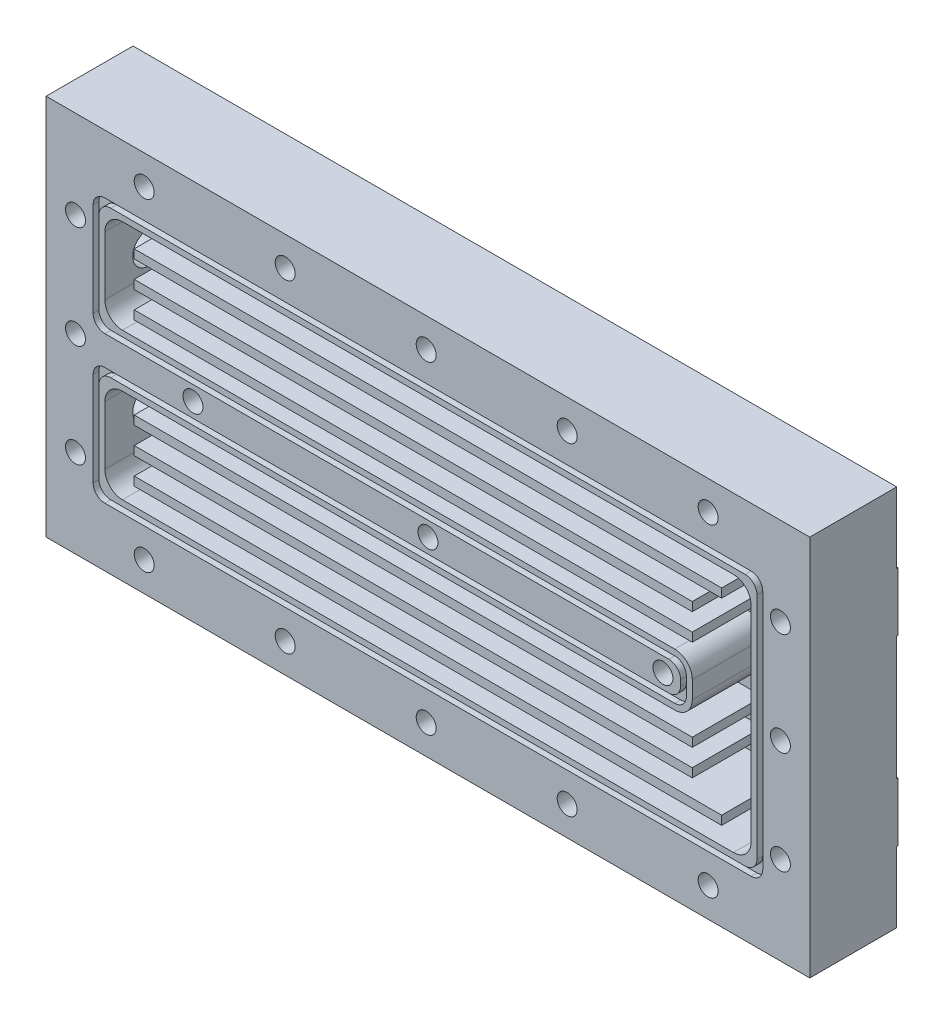
SolidWorks part; units mm, degrees
ref_plane "Plan de face" through (0, 0, 0) normal (0, 0, 1) x (1, 0, 0)
ref_plane "Plan de dessus" through (0, 0, 0) normal (0, 1, 0) x (1, 0, 0)
ref_plane "Plan de droite" through (0, 0, 0) normal (1, 0, 0) x (0, 0, -1)
sketch "Esquisse1" plane through (0, 0, 0) normal (0, 0, 1) x (1, 0, 0)
  line L1 (0, 0) -> (130, 0)
  line L2 (0, 0) -> (0, 65)
  line L3 (0, 65) -> (130, 65)
  line L4 (130, 0) -> (130, 65)
  dimension "D1" = 130
  dimension "D2" = 65
extrude "Boss.-Extru.1" add sketch "Esquisse1" along normal blind 14.8
sketch "Esquisse13" plane through (0, 0, 0) normal (0, 0, -1) x (-1, 0, 0)
  line L0 (-130, 0) -> (-130, 65) construction
  line L1 (-130, 53) -> (0, 53)
  line L2 (-130, 53) -> (-130, 43)
  line L3 (-130, 43) -> (0, 43)
  line L4 (0, 53) -> (0, 43)
  line L5 (0, 65) -> (0, 0) construction
  line L6 (-130, 65) -> (0, 65) construction
  line L7 (-130, 22) -> (0, 22)
  line L8 (-130, 22) -> (-130, 12)
  line L9 (-130, 12) -> (0, 12)
  line L10 (0, 22) -> (0, 12)
  line L11 (0, 0) -> (-130, 0) construction
  dimension "D1" = 10
  dimension "D2" = 10
  dimension "D3" = 12
  dimension "D4" = 12
extrude "Boss.-Extru.3" add sketch "Esquisse13" along normal blind 0.2
sketch "Esquisse2" plane through (0, 0, 14.8) normal (0, 0, 1) x (1, 0, 0)
  line L0 (-5.5409, 60) -> (136.6271, 60) construction
  line L1 (-5.5409, 5) -> (135.6371, 5) construction
  line L2 (130, 65) -> (0, 65) construction
  line L3 (0, 0) -> (130, 0) construction
  line L4 (0, 65) -> (0, 0) construction
  circle A0 centre (16.7, 60) radius 1
  circle A1 centre (40.7, 60) radius 1
  circle A2 centre (64.7, 60) radius 1
  circle A3 centre (88.7, 60) radius 1
  circle A4 centre (112.7, 60) radius 1
  circle A6 centre (16.7, 5) radius 1
  circle A7 centre (40.7, 5) radius 1
  circle A8 centre (64.7, 5) radius 1
  circle A9 centre (88.7, 5) radius 1
  circle A10 centre (112.7, 5) radius 1
  point P19 (0, 0)
  point P33 (0, 0)
  point P34 (49.9853, 3.1391)
  dimension "D3" = 16.7
  dimension "D9" = 24
  dimension "D1" = 5
  dimension "D2" = 5
  dimension "D4" = 24
  dimension "D5" = 24
  dimension "D6" = 24
  dimension "D7" = 24
  dimension "D8" = 24
  dimension "D10" = 24
  dimension "D11" = 24
  dimension "D12" = 16.7
hole_wizard "Dégagement M31" positions "Esquisse14" profile "Esquisse15" hole size "M3" standard "ISO" end condition through all
sketch "Esquisse14" plane through (0, 0, 14.8) normal (0, 0, 1) x (1, 0, 0)
  point P0 (16.7, 60)
  point P3 (40.7, 60)
  point P6 (64.7, 60)
  point P9 (88.7, 60)
  point P12 (112.7, 60)
  point P21 (112.7, 5)
  point P24 (88.7, 5)
  point P27 (64.7, 5)
  point P30 (40.7, 5)
  point P33 (16.7, 5)
sketch "Esquisse15" plane through (16.7, 60, 14.8) normal (1, 0, 0) x (0, -1, 0)
  line L0 (0, 0) -> (0, 15)
  line L1 (0, 15) -> (1.7, 15)
  line L2 (1.7, 15) -> (1.7, 0)
  line L5 (1.7, 0) -> (0, 0)
  line L11 (0, -6.35) -> (0, 107.95) construction
  dimension "Diamètre du perçage jusqu'au prochain" = 3.4
  dimension "Profondeur du perçage jusqu'au prochain" = 15
sketch "Esquisse6" plane through (0, 0, 14.8) normal (0, 0, 1) x (1, 0, 0)
  line L0 (13, 53) -> (117, 53)
  line L1 (120, 50) -> (120, 15)
  line L2 (117, 12) -> (13, 12)
  line L3 (10, 15) -> (10, 25)
  line L4 (13, 28) -> (107, 28)
  line L5 (110, 31) -> (110, 34)
  line L6 (107, 37) -> (13, 37)
  line L7 (10, 40) -> (10, 50)
  line L8 (130, 0) -> (130, 65) construction
  line L9 (0, 0) -> (130, 0) construction
  line L10 (130, 65) -> (0, 65) construction
  line L11 (0, 65) -> (0, 0) construction
  arc A0 (117, 53) -> (120, 50) centre (117, 50) cw
  arc A1 (110, 34) -> (107, 37) centre (107, 34) ccw
  arc A2 (107, 28) -> (110, 31) centre (107, 31) ccw
  arc A3 (120, 15) -> (117, 12) centre (117, 15) cw
  arc A4 (13, 12) -> (10, 15) centre (13, 15) cw
  arc A5 (10, 25) -> (13, 28) centre (13, 25) cw
  arc A6 (13, 37) -> (10, 40) centre (13, 40) cw
  arc A7 (13, 53) -> (10, 50) centre (13, 50) ccw
  dimension "D9" = 3
  dimension "D1" = 10
  dimension "D2" = 10
  dimension "D3" = 12
  dimension "D4" = 16
  dimension "D5" = 12
  dimension "D6" = 16
  dimension "D7" = 10
  dimension "D8" = 10
extrude "Enlèv. mat.-Extru.6" cut sketch "Esquisse6" against normal blind 12
sketch "Esquisse7" plane through (0, 0, 0) normal (-1, 0, 0) x (0, 0, 1)
  line L0 (14.8, 65) -> (14.8, 0) construction
  line L1 (14.8, 0) -> (0, 0) construction
  line L2 (14.8, 65) -> (0, 65) construction
  circle A0 centre (7.3, 44) radius 2.7
  circle A1 centre (7.3, 21) radius 2.7
  dimension "D1" = 7.5
  dimension "D2" = 7.5
  dimension "D3" = 21
  dimension "D4" = 21
hole_wizard "Dégagement M51" positions "Esquisse8" profile "Esquisse9" hole size "M5" standard "ISO" end condition up to next
sketch "Esquisse8" plane through (0, 0, 0) normal (-1, 0, 0) x (0, 0, 1)
  point P0 (7.3, 44)
  point P3 (7.3, 21)
sketch "Esquisse9" plane through (0, 44, 7.3) normal (0, 1, 0) x (0, 0, 1)
  line L0 (0, 0) -> (0, 10)
  line L1 (0, 10) -> (2.75, 10)
  line L2 (2.75, 10) -> (2.75, 0)
  line L5 (2.75, 0) -> (0, 0)
  line L11 (0, -6.35) -> (0, 107.95) construction
  dimension "Diamètre du perçage jusqu'au prochain" = 5.5
  dimension "Profondeur du perçage jusqu'au prochain" = 10
sketch "Esquisse10" plane through (0, 0, 0) normal (-1, 0, 0) x (0, 0, 1)
  circle A0 centre (7.3, 21) radius 4
  circle A1 centre (7.3, 44) radius 4
extrude "Enlèv. mat.-Extru.7" cut sketch "Esquisse10" against normal blind 2
sketch "Esquisse11" plane through (0, 0, 14.8) normal (0, 0, 1) x (1, 0, 0)
  line L1 (11, 54) -> (119, 54)
  line L3 (11, 11) -> (119, 11)
  line L4 (121, 52) -> (121, 13)
  line L5 (120, 10) -> (10, 10)
  line L6 (122, 12) -> (122, 53)
  line L7 (120, 55) -> (10, 55)
  line L11 (117, 53) -> (13, 53) construction
  line L12 (9, 13) -> (9, 27)
  line L13 (11, 29) -> (107, 29)
  line L14 (109, 31) -> (109, 34)
  line L15 (107, 36) -> (11, 36)
  line L16 (9, 38) -> (9, 52)
  line L17 (13, 37) -> (107, 37) construction
  line L18 (10, 50) -> (10, 40) construction
  line L19 (110, 34) -> (110, 31) construction
  line L20 (120, 15) -> (120, 50) construction
  line L21 (8, 12) -> (8, 28)
  line L22 (10, 30) -> (106, 30)
  line L23 (108, 32) -> (108, 33)
  line L24 (106, 35) -> (10, 35)
  line L25 (8, 37) -> (8, 53)
  line L26 (13, 12) -> (117, 12) construction
  line L27 (10, 25) -> (10, 15) construction
  line L29 (107, 28) -> (13, 28) construction
  arc A0 (122, 53) -> (120, 55) centre (120, 53) ccw
  arc A1 (119, 54) -> (121, 52) centre (119, 52) cw
  arc A2 (120, 10) -> (122, 12) centre (120, 12) ccw
  arc A3 (119, 11) -> (121, 13) centre (119, 13) ccw
  arc A4 (9, 13) -> (11, 11) centre (11, 13) ccw
  arc A8 (109, 34) -> (107, 36) centre (107, 34) ccw
  arc A9 (107, 29) -> (109, 31) centre (107, 31) ccw
  arc A10 (9, 27) -> (11, 29) centre (11, 27) cw
  arc A11 (11, 36) -> (9, 38) centre (11, 38) cw
  arc A12 (108, 33) -> (106, 35) centre (106, 33) ccw
  arc A13 (106, 30) -> (108, 32) centre (106, 32) ccw
  arc A14 (8, 28) -> (10, 30) centre (10, 28) cw
  arc A15 (10, 35) -> (8, 37) centre (10, 37) cw
  arc A16 (10, 10) -> (8, 12) centre (10, 12) cw
  arc A17 (8, 53) -> (10, 55) centre (10, 53) cw
  arc A18 (11, 54) -> (9, 52) centre (11, 52) ccw
  point P0 (9, 53.858)
  point P5 (3, 55)
  point P7 (3, 10)
  point P19 (3.0651, 55)
  point P62 (4.7733, 10)
  point P65 (3, 10.0733)
  dimension "D1" = 2
  dimension "D3" = 2
  dimension "D9" = 2
  dimension "D20" = 2
  dimension "D21" = 2
  dimension "D2" = 1
  dimension "D4" = 1
  dimension "D5" = 1
  dimension "D6" = 1
  dimension "D7" = 1
  dimension "D8" = 1
  dimension "D10" = 1
  dimension "D11" = 1
  dimension "D12" = 1
  dimension "D13" = 1
  dimension "D14" = 1
  dimension "D15" = 1
  dimension "D16" = 1
  dimension "D17" = 1
  dimension "D18" = 1
  dimension "D19" = 1
extrude "Enlèv. mat.-Extru.9" cut sketch "Esquisse11" against normal blind 1
sketch "Esquisse12" plane through (0, 0, 2.8) normal (0, 0, 1) x (1, 0, 0)
  line L23 (15, 1.4564) -> (15, 62.6625) construction
  line L24 (10, 50) -> (10, 40) construction
  line L25 (15, 16.5) -> (115, 16.5)
  line L26 (15, 16.5) -> (15, 15)
  line L27 (15, 15) -> (115, 15)
  line L28 (115, 16.5) -> (115, 15)
  line L29 (15, 21) -> (110, 21)
  line L30 (15, 21) -> (15, 19.5)
  line L31 (15, 19.5) -> (110, 19.5)
  line L32 (110, 21) -> (110, 19.5)
  line L33 (15, 25.5) -> (110, 25.5)
  line L34 (15, 25.5) -> (15, 24)
  line L35 (15, 24) -> (110, 24)
  line L36 (110, 25.5) -> (110, 24)
  line L37 (15, 39.5) -> (110, 39.5)
  line L38 (15, 39.5) -> (15, 41)
  line L39 (15, 41) -> (110, 41)
  line L40 (110, 39.5) -> (110, 41)
  line L41 (15, 44) -> (110, 44)
  line L42 (15, 44) -> (15, 45.5)
  line L43 (15, 45.5) -> (110, 45.5)
  line L44 (110, 44) -> (110, 45.5)
  line L45 (15, 50) -> (115, 50)
  line L46 (15, 50) -> (15, 48.5)
  line L47 (15, 48.5) -> (115, 48.5)
  line L48 (115, 50) -> (115, 48.5)
  line L49 (117, 53) -> (13, 53) construction
  line L52 (13, 12) -> (117, 12) construction
  dimension "D1" = 5
  dimension "D2" = 95
  dimension "D3" = 95
  dimension "D4" = 100
  dimension "D5" = 1.5
  dimension "D6" = 1.5
  dimension "D7" = 1.5
  dimension "D8" = 1.5
  dimension "D9" = 1.5
  dimension "D10" = 1.5
  dimension "D11" = 95
  dimension "D12" = 95
  dimension "D13" = 100
  dimension "D14" = 3
  dimension "D15" = 3
  dimension "D16" = 3
  dimension "D17" = 3
  dimension "D18" = 3
  dimension "D19" = 3
extrude "Boss.-Extru.2" add sketch "Esquisse12" along normal blind 12
sketch "Esquisse16" plane through (0, 0, 14.8) normal (0, 0, 1) x (1, 0, 0)
  line L0 (0, 65) -> (0, 0) construction
  line L1 (130, 0) -> (130, 65) construction
  line L2 (0, 0) -> (130, 0) construction
  line L3 (130, 65) -> (0, 65) construction
  circle A0 centre (5, 50) radius 1
  circle A1 centre (5, 15) radius 1
  circle A2 centre (25, 32.5) radius 1
  circle A3 centre (65, 32.5) radius 1
  circle A4 centre (105, 32.5) radius 1
  circle A5 centre (125, 50) radius 1
  circle A6 centre (125, 15) radius 1
  circle A7 centre (5, 32.5) radius 1
  circle A8 centre (125, 32.5) radius 1
  dimension "D1" = 5
  dimension "D15" = 5
  dimension "D16" = 20
  dimension "D2" = 5
  dimension "D3" = 5
  dimension "D4" = 5
  dimension "D5" = 15
  dimension "D6" = 15
  dimension "D7" = 15
  dimension "D8" = 15
  dimension "D9" = 32.5
  dimension "D10" = 20
  dimension "D11" = 40
  dimension "D12" = 32.5
  dimension "D13" = 32.5
  dimension "D14" = 40
  dimension "D17" = 32.5
hole_wizard "Dégagement M32" positions "Esquisse17" profile "Esquisse19" hole size "M3" standard "ISO"
sketch "Esquisse17" plane through (0, 0, 14.8) normal (0, 0, 1) x (1, 0, 0)
  point P0 (5, 50)
  point P3 (5, 15)
  point P6 (25, 32.5)
  point P9 (65, 32.5)
  point P12 (105, 32.5)
  point P15 (125, 15)
  point P18 (125, 50)
  point P22 (5, 32.5)
  point P25 (125, 32.5)
sketch "Esquisse19" plane through (5, 50, 14.8) normal (1, 0, 0) x (0, -1, 0)
  line L0 (0, 0) -> (0, 10)
  line L1 (0, 10) -> (1.7, 8.9785)
  line L2 (1.7, 8.9785) -> (1.7, 0)
  line L5 (1.7, 0) -> (0, 0)
  line L10 (0, 10) -> (-1.7, 8.9785) construction
  line L11 (0, -6.35) -> (0, 107.95) construction
  dimension "Diamètre du perçage" = 3.4
  dimension "Profondeur du perçage" = 10
  dimension "Angle de pointe" = 118
